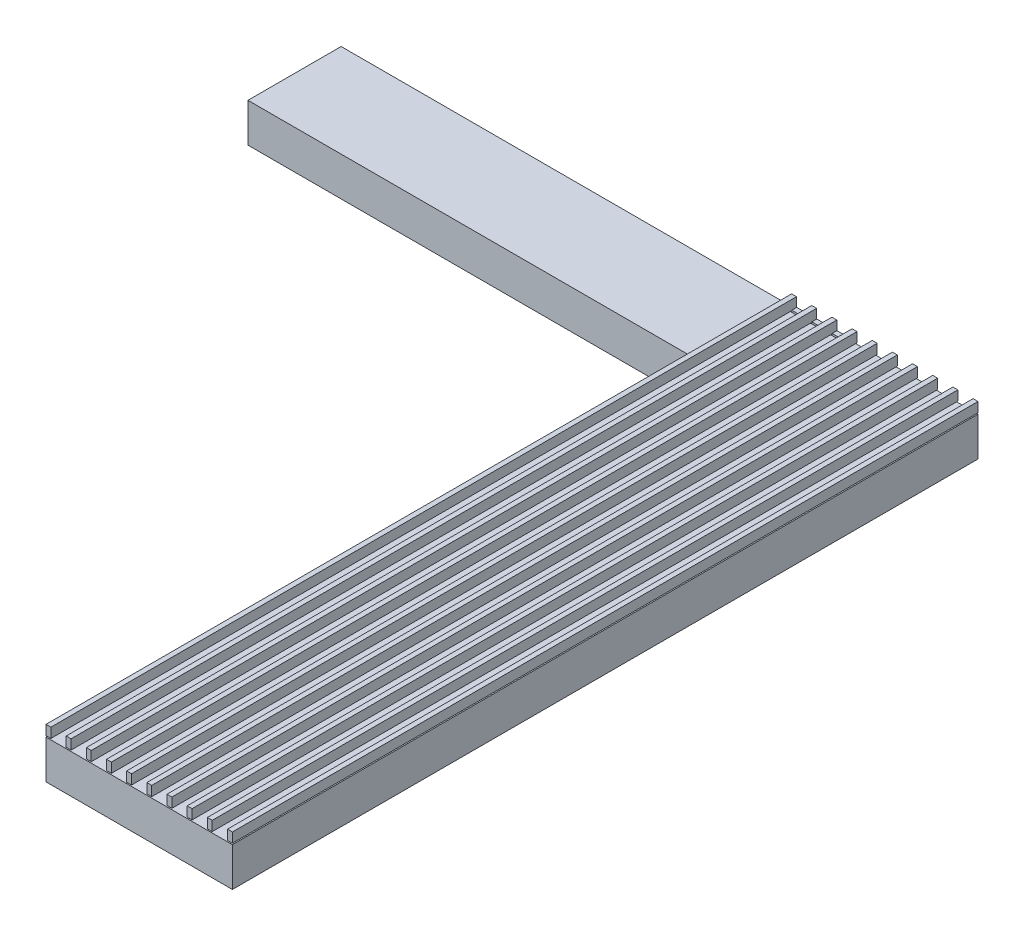
SolidWorks part; units mm, degrees
other "Wall"
other "mount"
ref_plane "Front Plane" through (0, 0, 0) normal (0, 0, 1) x (1, 0, 0)
ref_plane "Top Plane" through (0, 0, 0) normal (0, 1, 0) x (1, 0, 0)
ref_plane "Right Plane" through (0, 0, 0) normal (1, 0, 0) x (0, 0, -1)
sketch "Sketch1" plane through (0, 0, 0) normal (0, 1, 0) x (1, 0, 0)
  line L1 (0, 0) -> (609.6, 0)
  line L2 (0, 0) -> (0, 2438.4)
  line L3 (0, 2438.4) -> (609.6, 2438.4)
  line L4 (609.6, 0) -> (609.6, 2438.4)
  dimension "D1" = 609.6
  dimension "D2" = 2438.4
extrude "Boss-Extrude1" add sketch "Sketch1" along normal blind 127 contours L2 L3 L4 L1
ref_plane "Plane1" through (0, 131, 0) normal (0, 1, 0) x (1, 0, 0)
sketch "Sketch2" plane through (0, 131, 0) normal (0, 1, 0) x (1, 0, 0)
  line L0 (0, 0) -> (609.6, 0) construction
  line L1 (0, 2438.4) -> (16, 2438.4)
  line L2 (0, 2438.4) -> (0, 0)
  line L3 (0, 0) -> (16, 0)
  line L4 (16, 2438.4) -> (16, 0)
  dimension "D1" = 16
extrude "Boss-Extrude2" add sketch "Sketch2" along normal blind 32 separate body
pattern_linear "LPattern2" count 10 spacing 65.9556 along (1, 0, 0) of "Boss-Extrude2"
sketch "Sketch3" plane through (0, 0, 0) normal (-1, 0, 0) x (0, 0, 1)
  line L0 (0, 127) -> (-2438.4, 127) construction
  line L1 (-2438.4, 0) -> (-2133.6, 0)
  line L2 (-2438.4, 0) -> (-2438.4, 127)
  line L3 (-2438.4, 127) -> (-2133.6, 127)
  line L4 (-2133.6, 0) -> (-2133.6, 127)
  dimension "D1" = 304.8
extrude "Boss-Extrude3" add sketch "Sketch3" along normal blind 1473.2 separate body
sketch "Sketch4" plane through (0, 0, -2438.4) normal (0, 0, -1) x (-1, 0, 0)
  line L0 (0, 130) -> (-16.5, 130)
  line L1 (-16.5, 130) -> (-16.5, 133)
  line L2 (-16.5, 133) -> (-65.4556, 133)
  line L3 (-65.4556, 133) -> (-65.4556, 130)
  line L4 (-65.9556, 163) -> (-65.9556, 131) construction
  line L5 (335.28, 131) -> (-335.28, 131) construction
  line L6 (-16, 163) -> (-16, 131) construction
  line L7 (0, 163) -> (0, 131) construction
  line L8 (-65.4556, 130) -> (-65.9556, 130)
  line L9 (-65.9556, 130) -> (-82.4556, 130)
  line L10 (-82.4556, 130) -> (-82.4556, 133)
  line L11 (-82.4556, 133) -> (-131.4111, 133)
  line L12 (-131.4111, 133) -> (-131.4111, 130)
  line L13 (-131.4111, 130) -> (-131.9111, 130)
  line L14 (-131.9111, 130) -> (-148.4111, 130)
  line L15 (-148.4111, 130) -> (-148.4111, 133)
  line L16 (-148.4111, 133) -> (-197.3667, 133)
  line L17 (-197.3667, 133) -> (-197.3667, 130)
  line L18 (-197.3667, 130) -> (-197.8667, 130)
  line L20 (-81.9556, 163) -> (-81.9556, 131) construction
  line L21 (0, 130) -> (0, 127)
  line L22 (0, 127) -> (-197.8667, 127)
  line L23 (0, 127) -> (-609.6, 127) construction
  line L24 (-197.8667, 127) -> (-197.8667, 130)
  dimension "D1" = 0.5
  dimension "D2" = 2
  dimension "D3" = 0.5
  dimension "D4" = 1
  dimension "D5" = 6
  dimension "D6" = 0
  dimension "D7" = 0
  dimension "D8" = 65.9556
  dimension "D13" = 0.5
  dimension "D9" = 3
extrude "Boss-Extrude4" add sketch "Sketch4" against normal blind 16 separate body
sketch "Sketch5" plane through (0, 133, 0) normal (0, 1, 0) x (1, 0, 0)
  line L0 (106.9333, 2422.4) -> (106.9333, 2438.4) construction
  line L3 (82.4556, 2422.4) -> (131.4111, 2422.4) construction
  line L6 (82.4556, 2438.4) -> (131.4111, 2438.4) construction
  line L7 (131.4111, 2430.4) -> (82.4556, 2430.4) construction
  line L8 (131.4111, 2422.4) -> (131.4111, 2438.4) construction
  line L9 (82.4556, 2422.4) -> (82.4556, 2438.4) construction
  circle A1 centre (106.9333, 2430.4) radius 2
  point P12 (106.9333, 2430.4)
  point P13 (106.9333, 2430.4)
  dimension "D1" = 4
extrude "Cut-Extrude1" cut sketch "Sketch5" against normal up to next (6 mm away)
sketch "Sketch6" plane through (0, 133, 0) normal (0, 1, 0) x (1, 0, 0)
  circle A0 centre (106.9333, 2430.4) radius 2 construction
  circle A1 centre (106.9333, 2430.4) radius 2 construction
  circle A2 centre (106.9333, 2430.4) radius 4
  dimension "D1" = 8
extrude "Cut-Extrude2" cut sketch "Sketch6" against normal blind 3
